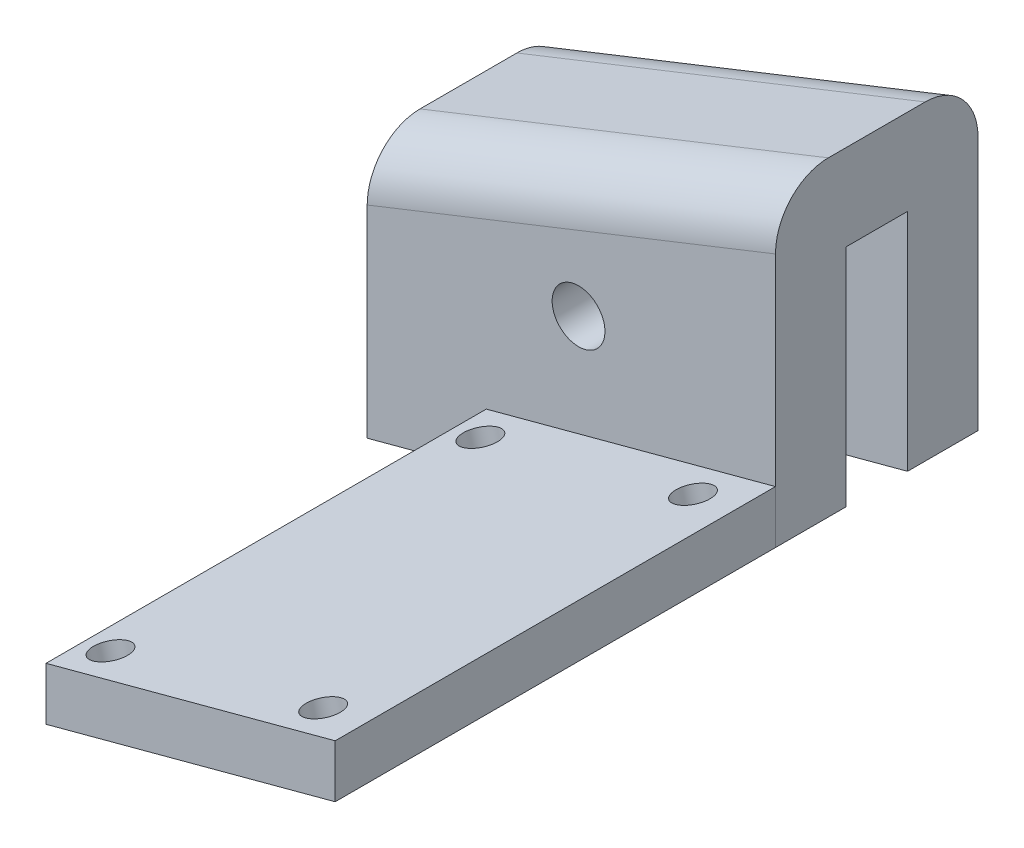
SolidWorks part; units mm, degrees
material "20% infill ABS"
ref_plane "Front" through (0, 0, 0) normal (0, 0, 1) x (1, 0, 0)
ref_plane "Top" through (0, 0, 0) normal (0, 1, 0) x (1, 0, 0)
ref_plane "Right" through (0, 0, 0) normal (1, 0, 0) x (0, 0, -1)
sketch "Sketch1" plane through (0, 0, 0) normal (0, 0, 1) x (1, 0, 0)
  line L0 (174.195, -57.9822) -> (197.3772, -51.7705) construction
  line L1 (174.195, -57.9822) -> (197.3772, -51.7705)
  line L2 (197.3772, -51.7705) -> (197.3772, -38.9869)
  line L3 (174.195, -57.9822) -> (174.195, -48.3476)
  line L4 (174.195, -48.3476) -> (174.195, -43.2884)
  line L5 (174.195, -43.2884) -> (197.3772, -34.1054)
  line L6 (197.3772, -34.1054) -> (197.3772, -38.9869)
  line L12 (83, 160.5) -> (80, 160.5)
  line L13 (80, 160.5) -> (80, 150.5)
  line L14 (80, 150.5) -> (83, 150.5)
  line L15 (83, 150.5) -> (83, 145.5)
  line L16 (288.0952, 47) -> (296.5952, 47)
  line L17 (296.5952, 47) -> (296.5952, 44)
  line L18 (296.5952, 44) -> (287.9228, 44)
  line L19 (155, -54.0482) -> (155, -59.5)
  line L20 (155, -59.5) -> (152, -59.5)
  line L21 (152, -59.5) -> (152, -64.5)
  line L22 (152, -64.5) -> (155, -64.5)
  line L23 (155, -64.5) -> (155, -69.5)
  parabola Q1 (155, -69.5) -> (306.0893, 45.5) focus (179.0197, 57.3821) apex (244.7409, -27.552)
  spline S3 degree 3 poles (1082.6403, 119.8012) (-59.8122, 135.2579) (25.754, 146.2701) (93.6051, 145.4111) (101.0301, 145.2187) (109.751, 144.8283) (121.1337, 144.0897) (134.8993, 142.7481) (150.6813, 140.4388) (165.7317, 137.4023) (184.8372, 132.3478) (206.9506, 124.0773) (226.87, 112.9967) (241.6235, 102.2656) (252.1296, 93.2247) (262.1032, 83.1283) (269.9863, 73.7793) (276.0412, 65.7051) (280.4563, 59.3453) (284.0332, 53.781) (313.705, 4.8935) (336.7745, -69.706) (-256.1123, 885.9429) knots -0.616449 -0.616449 -0.616449 -0.616449 0.021043 0.036204 0.066527 0.09685 0.127172 0.187818 0.248463 0.309108 0.369753 0.491044 0.612334 0.67298 0.733625 0.79427 0.854915 0.885238 0.91556 0.945883 0.961044 1.559542 1.559542 1.559542 1.559542 only from (83, 145.5) to (288.0952, 47)
  spline S4 degree 3 poles (-1946.8665, -3271.9683) (365.3963, 313.7167) (344.8985, 132.8506) (281.8406, 34.3146) (276.5289, 26.6313) (269.8307, 17.8876) (260.462, 6.8492) (247.9292, -5.7971) (231.5494, -19.1757) (213.7896, -30.7929) (197.7998, -39.024) (184.2693, -44.7413) (173.7484, -48.594) (164.6601, -51.442) (53.2207, -82.1961) (-124.6747, -54.5902) (3987.5461, 1087.346) knots 0.489781 0.489781 0.489781 0.489781 0.497845 0.497982 0.498256 0.49853 0.498805 0.499353 0.499901 0.50045 0.500998 0.501273 0.501547 0.501821 0.501958 0.509749 0.509749 0.509749 0.509749 only from (287.9228, 44) to (155, -54.0482)
  spline S5 degree 3 poles (333.6076, -954.1208) (479.3551, 668.8846) (173.237, 29.6941) (-912.6161, 67.0926) knots -1.605787 -1.605787 -1.605787 -1.605787 2.973187 2.973187 2.973187 2.973187 only from (306.0893, 45.5) to (83, 160.5)
  spline S7 degree 3 poles (197.3772, -38.9869) (196.3757, -39.4584) (192.0662, -41.4467) (184.4307, -44.6731) (177.5899, -47.1871) (174.195, -48.3476) knots 0.500915 0.500915 0.500915 0.500915 0.500998 0.501273 0.501534 0.501534 0.501534 0.501534 construction
  dimension "D1" = 0
extrude "Boss-Extrude1" add sketch "Sketch1" along normal blind 4
sketch "Sketch2" plane through (0, 0, 4) normal (0, 0, 1) x (1, 0, 0)
  line L0 (197.3772, -51.7705) -> (197.3772, -48.7705)
  line L1 (197.3772, -51.7705) -> (197.3772, -34.1054) construction
  line L2 (197.3772, -48.7705) -> (180.9564, -53.1705)
  line L3 (180.9564, -53.1705) -> (180.9564, -56.1705)
  line L4 (174.195, -57.9822) -> (197.3772, -51.7705) construction
  line L5 (174.195, -57.9822) -> (197.3772, -51.7705) construction
  line L6 (180.9564, -56.1705) -> (197.3772, -51.7705)
  dimension "D1" = 3
  dimension "D2" = 17
extrude "Boss-Extrude2" add sketch "Sketch2" along normal up to surface (25 mm away) separate body
sketch "Sketch3" plane through (26.1644, -97.6469, 0) normal (0.2588, -0.9659, 0) x (0.9659, 0.2588, 0)
  circle A0 centre (162.7525, 6) radius 1 construction
  circle A1 centre (162.7525, 27) radius 1 construction
  circle A2 centre (175.2525, 6) radius 1 construction
  circle A3 centre (175.2525, 27) radius 1 construction
  circle A4 centre (162.7525, 6) radius 1
  circle A5 centre (162.7525, 27) radius 1
  circle A6 centre (175.2525, 6) radius 1
  circle A7 centre (175.2525, 27) radius 1
extrude "Cut-Extrude1" cut sketch "Sketch3" against normal blind 34
sketch "Sketch4" plane through (0, 0, 0) normal (0, 0, -1) x (-1, 0, 0)
  line L0 (-197.3772, -34.1054) -> (-174.195, -43.2884)
  line L1 (-174.195, -43.2884) -> (-174.195, -48.3476)
  line L2 (-174.195, -43.2884) -> (-174.195, -57.9822) construction
  line L3 (-197.3772, -34.1054) -> (-197.3772, -38.9869)
  line L4 (-197.3772, -51.7705) -> (-197.3772, -34.1054) construction
  line L17 (-80, 160.5) -> (-83, 160.5)
  line L18 (-80, 150.5) -> (-80, 160.5)
  line L19 (-83, 150.5) -> (-80, 150.5)
  line L20 (-83, 145.5) -> (-83, 150.5)
  line L21 (-296.5952, 47) -> (-288.0952, 47)
  line L22 (-296.5952, 44) -> (-296.5952, 47)
  line L23 (-287.9228, 44) -> (-296.5952, 44)
  line L24 (-155, -59.5) -> (-155, -54.0482)
  line L25 (-152, -59.5) -> (-155, -59.5)
  line L26 (-152, -64.5) -> (-152, -59.5)
  line L27 (-155, -64.5) -> (-152, -64.5)
  line L28 (-155, -69.5) -> (-155, -64.5)
  line L36 (-155, -59.5) -> (-155, -54.0482)
  line L37 (-152, -59.5) -> (-155, -59.5)
  line L38 (-152, -64.5) -> (-152, -59.5)
  line L39 (-155, -64.5) -> (-152, -64.5)
  line L40 (-155, -69.5) -> (-155, -64.5)
  parabola Q1 (-306.0893, 45.5) -> (-155, -69.5) focus (-179.0197, 57.3821) apex (-244.7409, -27.552)
  spline S3 degree 3 poles (256.1156, 885.9482) (-336.7745, -69.7062) (-313.705, 4.8934) (-284.0332, 53.781) (-280.4563, 59.3453) (-276.0412, 65.7051) (-269.9863, 73.7793) (-262.1032, 83.1283) (-252.1296, 93.2247) (-241.6235, 102.2656) (-226.87, 112.9967) (-206.9506, 124.0773) (-184.8372, 132.3478) (-165.7317, 137.4023) (-150.6813, 140.4388) (-134.8993, 142.7481) (-121.1337, 144.0897) (-109.751, 144.8283) (-101.0301, 145.2187) (-93.6051, 145.4111) (-25.7544, 146.2701) (59.8111, 135.258) (-1082.6172, 119.8015) knots -0.583337 -0.583337 -0.583337 -0.583337 0.015161 0.030323 0.060645 0.090968 0.12129 0.181936 0.242581 0.303226 0.363871 0.485162 0.606452 0.667098 0.727743 0.788388 0.849033 0.879356 0.909679 0.940001 0.955163 1.59265 1.59265 1.59265 1.59265 only from (-288.0952, 47) to (-83, 145.5)
  spline S4 degree 3 poles (-3987.5031, 1087.334) (124.6735, -54.5904) (-53.2211, -82.196) (-164.6601, -51.442) (-173.7484, -48.594) (-184.2693, -44.7413) (-197.7998, -39.024) (-213.7896, -30.7929) (-231.5494, -19.1757) (-247.9292, -5.7971) (-260.462, 6.8492) (-269.8307, 17.8876) (-276.5289, 26.6313) (-281.8406, 34.3146) (-344.8981, 132.8499) (-365.396, 313.7143) (1946.8201, -3271.8963) knots 0.490015 0.490015 0.490015 0.490015 0.497806 0.497943 0.498217 0.498491 0.498765 0.499314 0.499862 0.500411 0.500959 0.501233 0.501508 0.501782 0.501919 0.509983 0.509983 0.509983 0.509983 only from (-155, -54.0482) to (-287.9228, 44)
  spline S5 degree 3 poles (912.6271, 67.093) (-173.2309, 29.6899) (-479.3533, 668.8854) (-333.6092, -954.1027) knots -1.973203 -1.973203 -1.973203 -1.973203 2.60577 2.60577 2.60577 2.60577 only from (-83, 160.5) to (-306.0893, 45.5)
  spline S7 degree 3 poles (-174.195, -48.3476) (-177.5899, -47.1871) (-184.4307, -44.6731) (-192.0662, -41.4467) (-196.3757, -39.4584) (-197.3772, -38.9869) knots 0.49823 0.49823 0.49823 0.49823 0.498491 0.498765 0.498849 0.498849 0.498849 0.498849
  line M20 (-174.195, -43.2884) -> (-197.3772, -34.1054)
  line M21 (-197.3772, -34.1054) -> (-197.3772, -51.7705)
  line M23 (-174.195, -57.9822) -> (-174.195, -43.2884)
  dimension "D1" = 0
extrude "Boss-Extrude3" add sketch "Sketch4" along normal blind 3.5 contours S7 M23 M20 M21
sketch "Sketch5" plane through (0, 0, -3.5) normal (0, 0, -1) x (-1, 0, 0)
  line L4 (-174.195, -43.2884) -> (-197.3772, -34.1054)
  line L5 (-174.195, -57.9822) -> (-174.195, -43.2884)
  line L6 (-197.3772, -51.7705) -> (-174.195, -57.9822)
  line L7 (-197.3772, -34.1054) -> (-197.3772, -51.7705)
  line L8 (-174.195, -43.2884) -> (-197.3772, -34.1054)
  line L9 (-174.195, -57.9822) -> (-174.195, -43.2884)
  line L10 (-197.3772, -51.7705) -> (-174.195, -57.9822)
  line L11 (-197.3772, -34.1054) -> (-197.3772, -51.7705)
  dimension "D1" = 0
extrude "Boss-Extrude4" add sketch "Sketch5" along normal blind 4
sketch "Sketch6" plane through (0, 0, -7.5) normal (0, 0, -1) x (-1, 0, 0)
  circle A0 centre (-186.195, -45.9822) radius 1.5
  dimension "D3" = 3
  dimension "D1" = 12
  dimension "D2" = 12
extrude "Cut-Extrude2" cut sketch "Sketch6" against normal blind 34
fillet "Fillet1" radius 3 2 edges at (185.7861, -38.6969, -7.5) (185.7861, -38.6969, 4)
